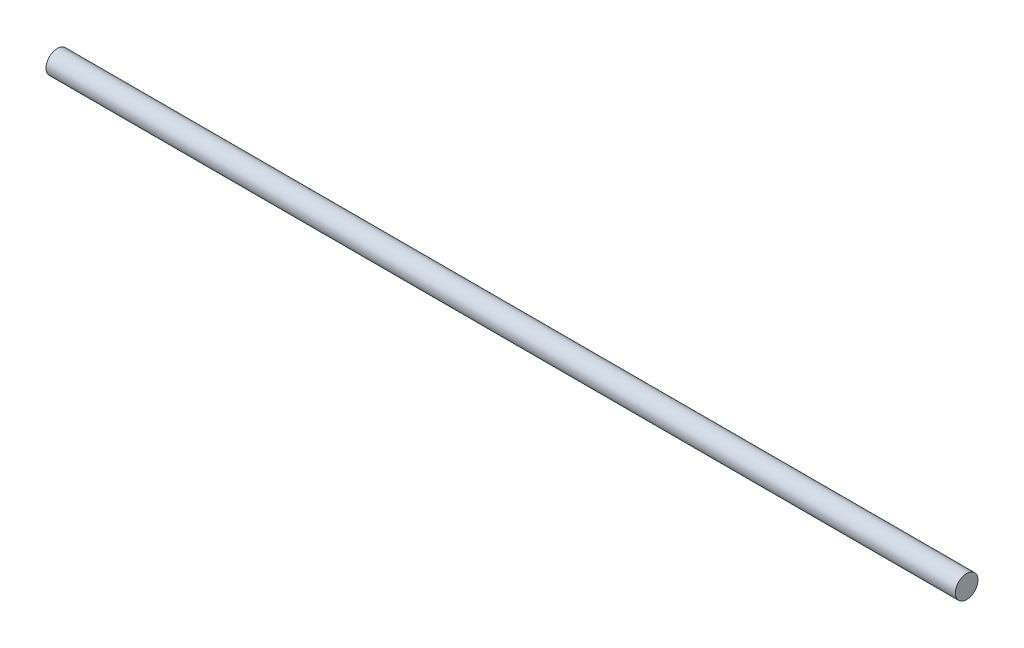
SolidWorks part; units mm, degrees
ref_plane "Front Plane" through (0, 0, 0) normal (0, 0, 1) x (1, 0, 0)
ref_plane "Top Plane" through (0, 0, 0) normal (0, 1, 0) x (1, 0, 0)
ref_plane "Right Plane" through (0, 0, 0) normal (1, 0, 0) x (0, 0, -1)
sketch "Sketch1" plane through (0, 0, 0) normal (1, 0, 0) x (0, 0, -1)
  circle A0 centre (0, 0) radius 24.95
  dimension "D1" = 49.9
extrude "Boss-Extrude1" add sketch "Sketch1" along normal blind 2000
